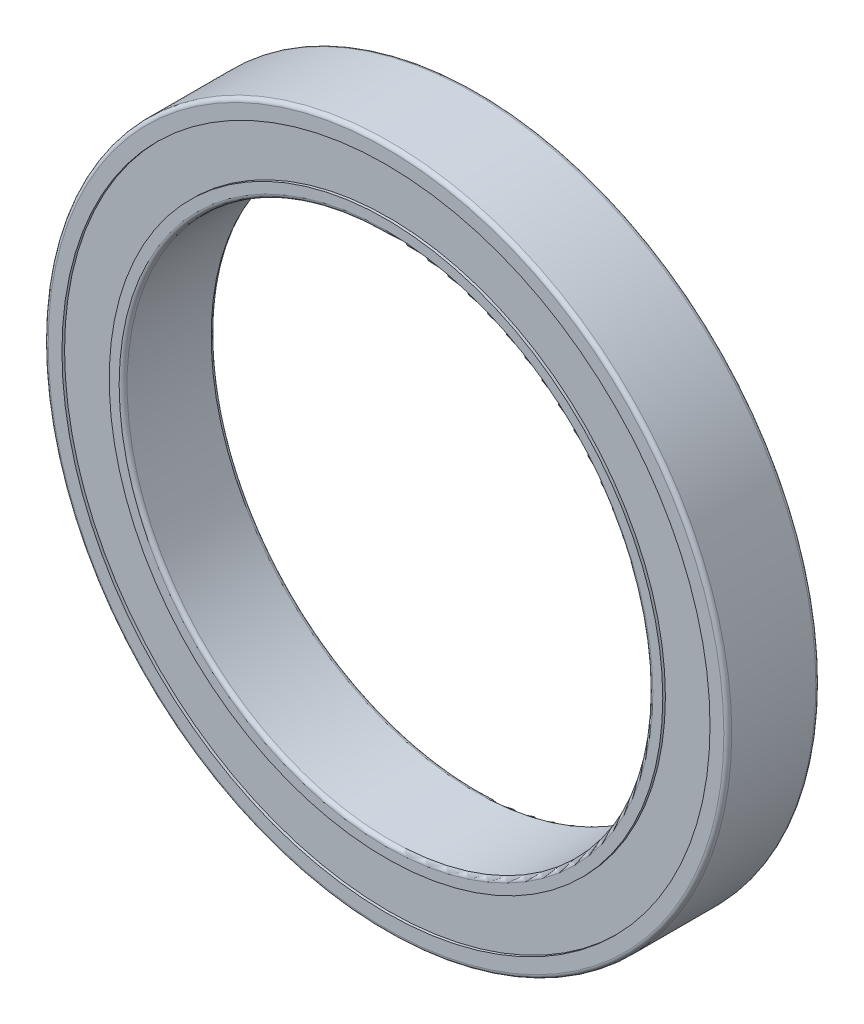
SolidWorks part; units mm, degrees
ref_plane "Front Plane" through (0, 0, 0) normal (0, 0, 1) x (1, 0, 0)
ref_plane "Top Plane" through (0, 0, 0) normal (0, 1, 0) x (1, 0, 0)
ref_plane "Right Plane" through (0, 0, 0) normal (1, 0, 0) x (0, 0, -1)
sketch "Sketch1" plane through (0, 0, 0) normal (1, 0, 0) x (0, 0, -1)
  line L0 (0, 0) -> (37.6864, 0) construction
  line L1 (-3.3407, 20) -> (3.0593, 20)
  line L2 (-3.6407, 20.3) -> (-3.6407, 25.7)
  line L3 (-3.3407, 26) -> (3.0593, 26)
  line L4 (3.3593, 20.3) -> (3.3593, 25.7)
  line L6 (-3.6407, 24.65) -> (-3.4407, 24.65)
  line L7 (-3.6407, 24.65) -> (-3.6407, 21.055)
  line L8 (-3.6407, 21.055) -> (-3.4407, 21.055)
  line L9 (3.3593, 24.65) -> (3.1593, 24.65)
  line L10 (3.3593, 24.65) -> (3.3593, 21.055)
  line L11 (3.3593, 21.055) -> (3.1593, 21.055)
  line L12 (3.1593, 24.65) -> (3.1593, 21.055)
  line L13 (-3.4407, 24.65) -> (-3.4407, 21.055)
  arc A0 (-3.3407, 26) -> (-3.6407, 25.7) centre (-3.3407, 25.7) ccw
  arc A1 (-3.6407, 20.3) -> (-3.3407, 20) centre (-3.3407, 20.3) ccw
  arc A2 (3.3593, 20.3) -> (3.0593, 20) centre (3.0593, 20.3) cw
  arc A3 (3.3593, 25.7) -> (3.0593, 26) centre (3.0593, 25.7) ccw
  point P7 (-3.6407, 26)
  point P14 (3.3593, 26)
  dimension "D4" = 0.3
  dimension "D1" = 7
  dimension "D2" = 20
  dimension "D3" = 26
  dimension "D5" = 3.595
  dimension "D6" = 21.055
  dimension "D7" = 0.2
revolve "Revolve1" add sketch "Sketch1" angle 360 about L0
